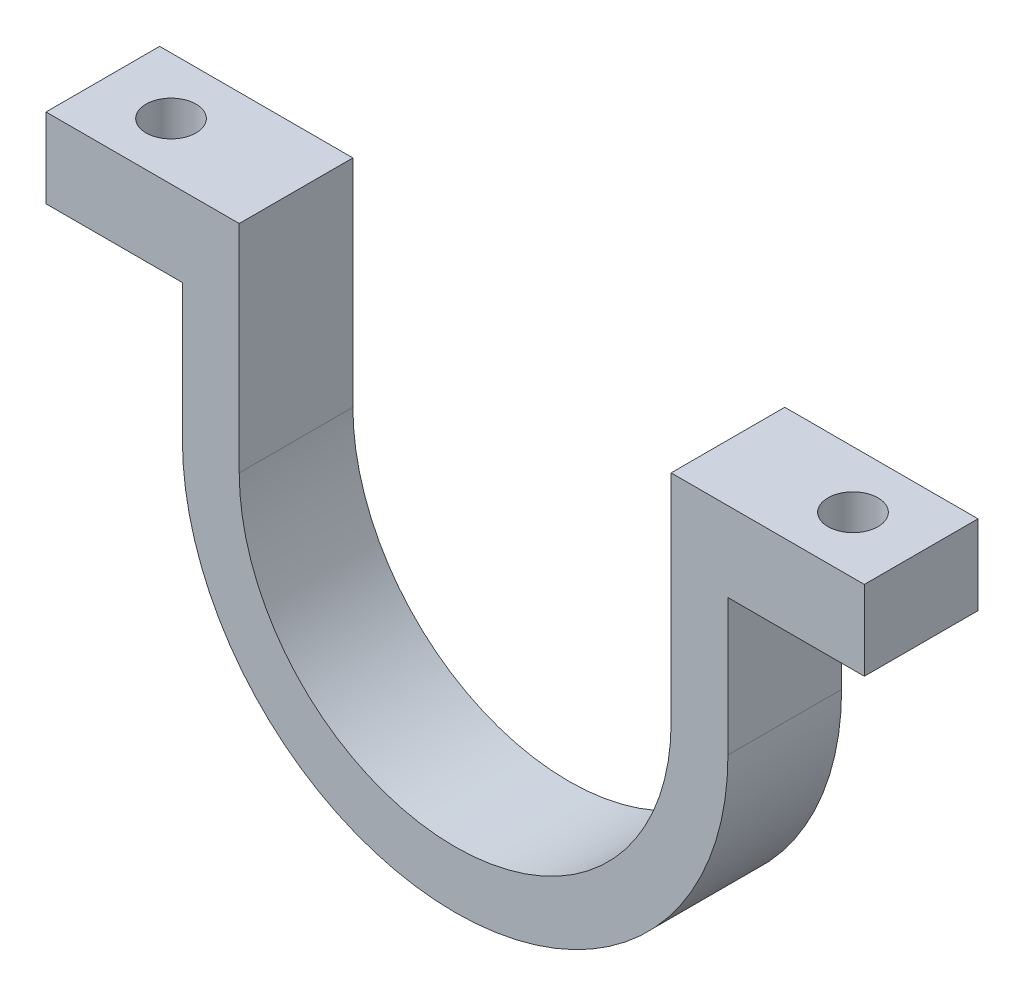
SolidWorks part; units mm, degrees
ref_plane "Plano frontal" through (0, 0, 0) normal (0, 0, 1) x (1, 0, 0)
ref_plane "Plano superior" through (0, 0, 0) normal (0, 1, 0) x (1, 0, 0)
ref_plane "Plano direito" through (0, 0, 0) normal (1, 0, 0) x (0, 0, -1)
sketch "Esboço1" plane through (0, 0, 0) normal (0, 0, 1) x (1, 0, 0)
  line L0 (-36, 19) -> (-19, 19)
  line L1 (-36, 12) -> (-24, 12)
  line L2 (24, 12) -> (36, 12)
  line L3 (-36, 12) -> (36, 12) construction
  line L4 (0, 24.5692) -> (0, 7.9539) construction
  line L8 (19, 19) -> (36, 19)
  line L9 (-36, 19) -> (36, 19) construction
  line L11 (-36, 19) -> (-36, 12)
  line L12 (36, 19) -> (36, 12)
  line L13 (-24, 0) -> (-24, 12)
  line L14 (24, 0) -> (24, 12)
  line L15 (-19, 0) -> (-19, 19)
  line L17 (19, 0) -> (19, 19)
  arc A0 (-19, 0) -> (19, 0) centre (0, 0) ccw
  arc A1 (-24, 0) -> (24, 0) centre (0, 0) ccw
  dimension "D1" = 38
  dimension "D4" = 5
  dimension "D2" = 12
  dimension "D3" = 7
extrude "Ressalto-extrusão1" add sketch "Esboço1" along normal blind 10
sketch "Esboço2" plane through (0, 19, 0) normal (0, 1, 0) x (1, 0, 0)
  line L0 (-24, -5) -> (-36, -5) construction
  line L1 (-24, -10) -> (-24, 0) construction
  line L2 (-36, -10) -> (-36, 0) construction
  line L3 (0, 0) -> (0, -10) construction
  line L4 (-24, -10) -> (24, -10) construction
  circle A0 centre (-30, -5) radius 2.2
  circle A1 centre (30, -5) radius 2.2
  dimension "D1" = 4.4
extrude "Corte-extrusão1" cut sketch "Esboço2" against normal blind 10
